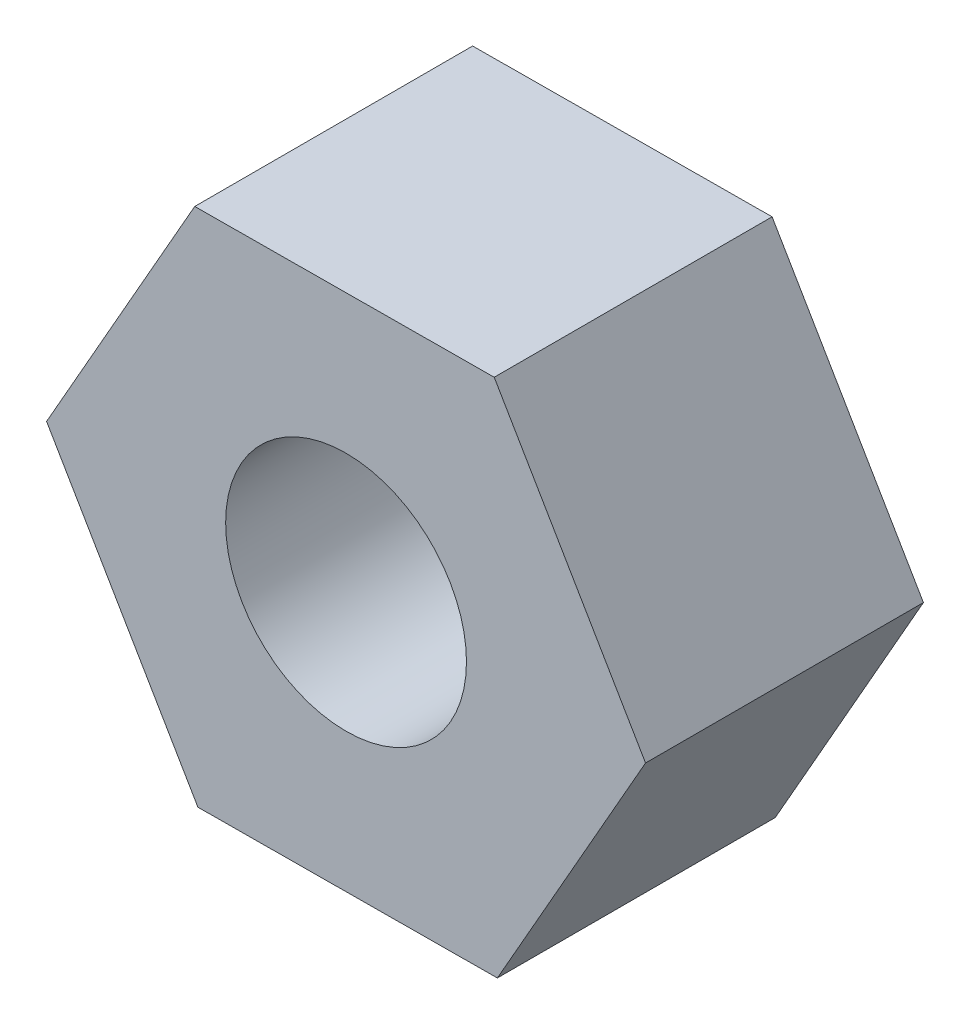
SolidWorks part; units mm, degrees
material "1.0558 (G300)"
ref_plane "Ön Düzlem" through (0, 0, 0) normal (0, 0, 1) x (1, 0, 0)
ref_plane "Üst Düzlem" through (0, 0, 0) normal (0, 1, 0) x (1, 0, 0)
ref_plane "Sağ Düzlem" through (0, 0, 0) normal (1, 0, 0) x (0, 0, -1)
sketch "Çizim1" plane through (0, 0, 0) normal (0, 0, 1) x (1, 0, 0)
  line L1 (8.168, -13.9505) -> (16.1655, 0.0984)
  line L2 (16.1655, 0.0984) -> (7.9975, 14.0489)
  line L3 (7.9975, 14.0489) -> (-8.168, 13.9505)
  line L4 (-8.168, 13.9505) -> (-16.1655, -0.0984)
  line L5 (-16.1655, -0.0984) -> (-7.9975, -14.0489)
  line L6 (-7.9975, -14.0489) -> (8.168, -13.9505)
  circle A0 centre (0, 0) radius 14 construction
  circle A1 centre (0, 0) radius 6.5
  dimension "D2" = 13
  dimension "D1" = 28
extrude "Yükseklik-Ekstrüzyon1" add sketch "Çizim1" along normal blind 15
